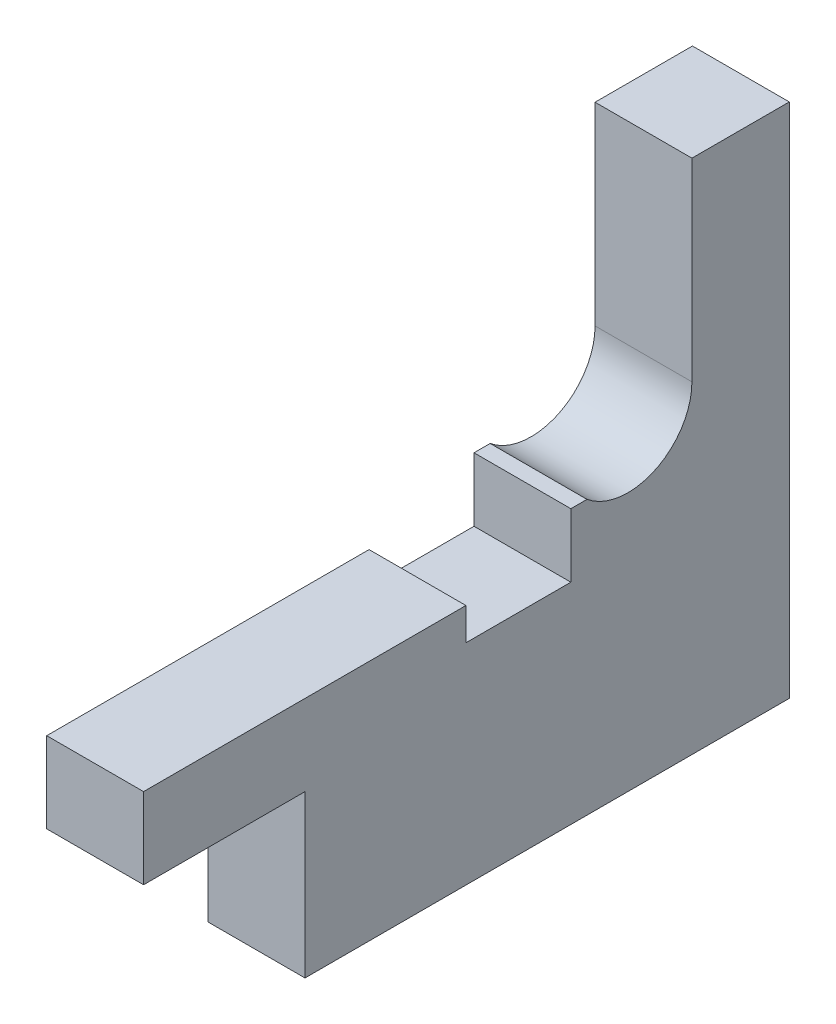
SolidWorks part; units mm, degrees
material "Plain Carbon Steel"
ref_plane "Front Plane" through (0, 0, 0) normal (0, 0, 1) x (1, 0, 0)
ref_plane "Top Plane" through (0, 0, 0) normal (0, 1, 0) x (1, 0, 0)
ref_plane "Right Plane" through (0, 0, 0) normal (1, 0, 0) x (0, 0, -1)
sketch "Sketch1" plane through (0, 0, 0) normal (1, 0, 0) x (0, 0, -1)
  line L0 (3.9688, 0) -> (3.9688, 12)
  line L1 (3.9688, 12) -> (10, 12)
  line L2 (10, 12) -> (10, -20)
  line L3 (10, -20) -> (-20, -20)
  line L4 (-20, -20) -> (-20, -10)
  line L5 (-20, -10) -> (-30, -10)
  line L6 (-30, -10) -> (-30, -5)
  line L10 (-30, -5) -> (-10.0312, -5)
  line L11 (-10.0312, -5) -> (-10.0312, -7)
  line L12 (-10.0312, -7) -> (-3.5312, -7)
  line L15 (-3.5312, -7) -> (-3.5312, -3.0568)
  line L17 (-3.5312, -3.0568) -> (-2.5312, -3.0568)
  arc A0 (-2.5312, -3.0568) -> (3.9688, 0) centre (0, 0) ccw
  dimension "D1" = 3.9688
  dimension "D2" = 30
  dimension "D3" = 32
  dimension "D4" = 5
  dimension "D5" = 10
  dimension "D6" = 10
  dimension "D7" = 12
  dimension "D8" = 10
  dimension "D9" = 1
  dimension "D10" = 6.5
  dimension "D11" = 2
  dimension "D12" = 6.5
extrude "Boss-Extrude1" add sketch "Sketch1" along normal blind 6 contours A0 L0 L1 L2 L3 L4 L5 L6 L10 L11 L12 L15 L17
